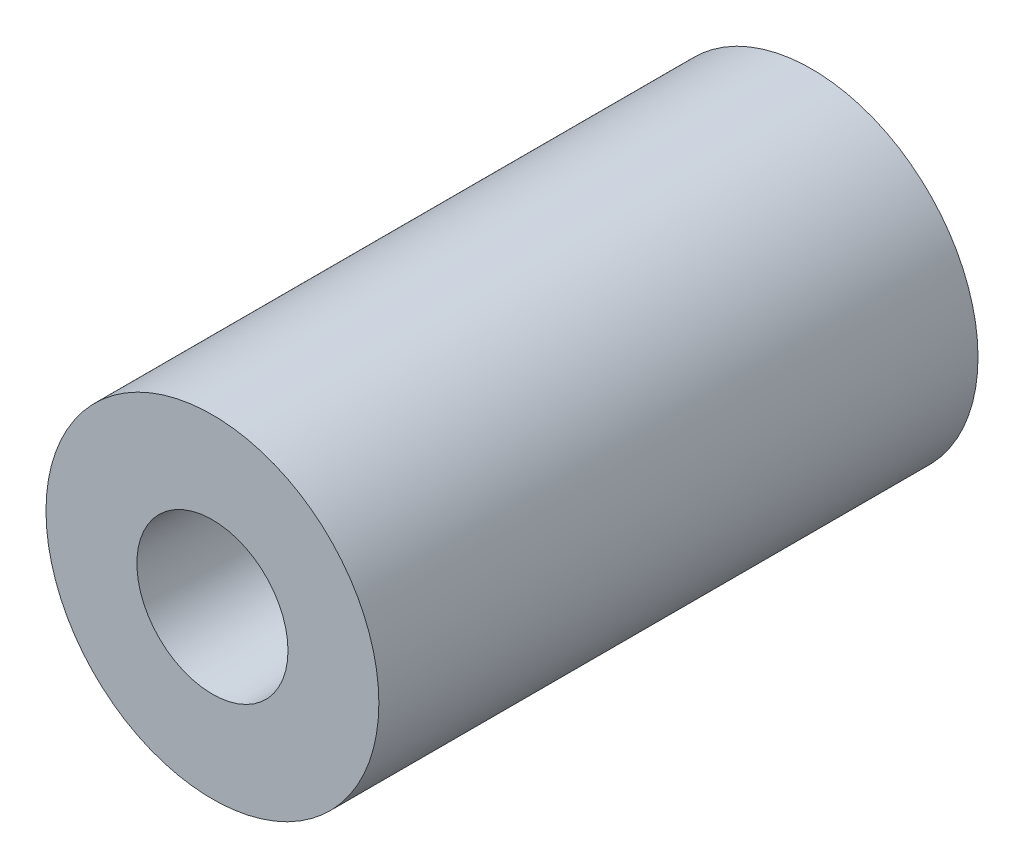
SolidWorks part; units mm, degrees
ref_plane "Front Plane" through (0, 0, 0) normal (0, 0, 1) x (1, 0, 0)
ref_plane "Top Plane" through (0, 0, 0) normal (0, 1, 0) x (1, 0, 0)
ref_plane "Right Plane" through (0, 0, 0) normal (1, 0, 0) x (0, 0, -1)
sketch "Sketch1" plane through (0, 0, 0) normal (0, 0, 1) x (1, 0, 0)
  circle A0 centre (0, 0) radius 5
  dimension "8mm" = 10
extrude "Boss-Extrude1" add sketch "Sketch1" along normal blind 18
sketch "Sketch2" plane through (0, 0, 0) normal (0, 0, 1) x (1, 0, 0)
  circle A0 centre (0, 0) radius 2.27
  dimension "D1" = 4.54
extrude "Cut-Extrude1" cut sketch "Sketch2" along a picked direction on the side of the normal blind 5.68 draft 3.074
sketch "Sketch7" plane through (0, 0, 0) normal (0, 0, 1) x (1, 0, 0)
  circle A0 centre (0, 0) radius 1
extrude "Cut-Extrude2" cut sketch "Sketch7" along normal through all
sketch "Sketch9" plane through (0, 0, 18) normal (0, 0, 1) x (1, 0, 0)
  circle A0 centre (0, 0) radius 2.27
  circle A1 centre (0, 0) radius 2.27 construction
extrude "Cut-Extrude3" cut sketch "Sketch9" against normal blind 5.68 draft 3.074
